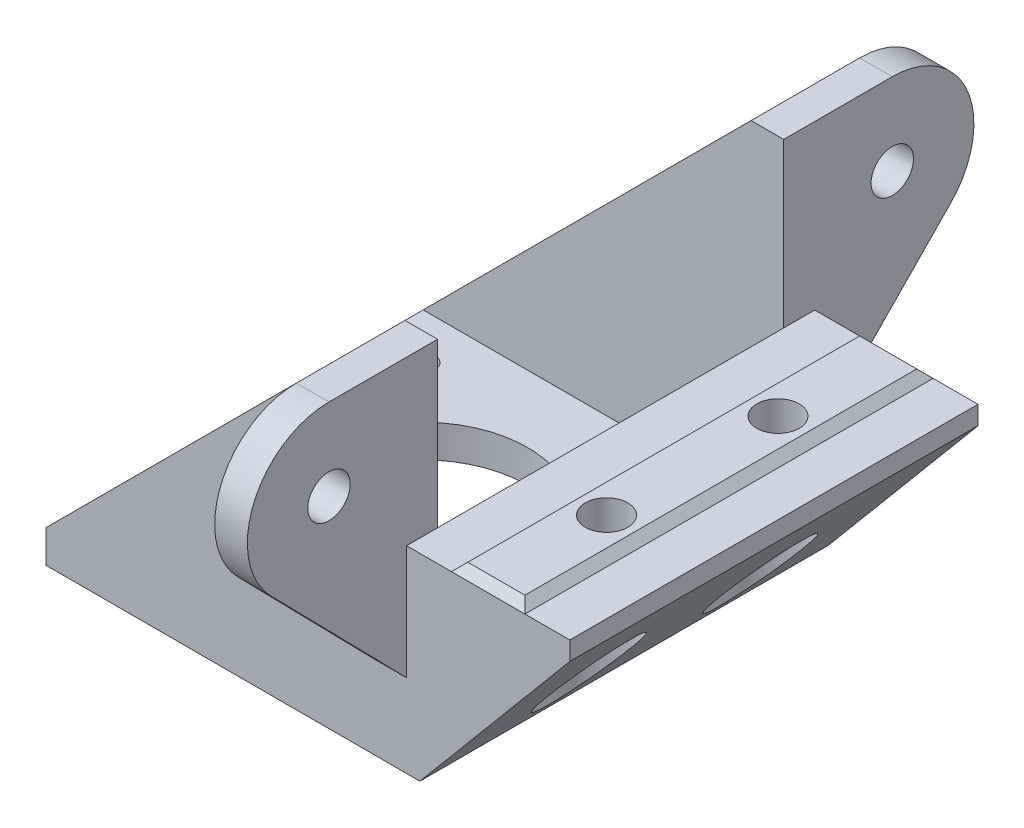
SolidWorks part; units mm, degrees
ref_plane "Front Plane" through (0, 0, 0) normal (0, 0, 1) x (1, 0, 0)
ref_plane "Top Plane" through (0, 0, 0) normal (0, 1, 0) x (1, 0, 0)
ref_plane "Right Plane" through (0, 0, 0) normal (1, 0, 0) x (0, 0, -1)
sketch "Sketch1" plane through (0, 0, 0) normal (0, 0, 1) x (1, 0, 0)
  line L0 (0, 0) -> (45.8, 0)
  line L1 (45.8, 0) -> (64.164, 21.8854)
  line L2 (64.164, 21.8854) -> (64.164, 24.164)
  line L3 (64.164, 24.164) -> (44.164, 24.164)
  line L4 (44.164, 44.164) -> (40.164, 44.164)
  line L5 (40.164, 44.164) -> (0, 4)
  line L6 (0, 4) -> (0, 0)
  line L7 (44.164, 24.164) -> (44.164, 44.164)
  dimension "D1" = 4
  dimension "D2" = 45.8
  dimension "D3" = 135
  dimension "D4" = 50
  dimension "D5" = 44.164
  dimension "D6" = 20
  dimension "D7" = 20
  dimension "D8" = 4
extrude "Boss-Extrude1" add sketch "Sketch1" against normal blind 3.8
sketch "Sketch2" plane through (0, 0, 0) normal (0, -1, 0) x (1, 0, 0)
  line L0 (0, 0) -> (45.8, 0)
  line L1 (45.8, 0) -> (45.8, -50)
  line L2 (45.8, -50) -> (0, -50)
  line L3 (0, -50) -> (0, 0)
  dimension "D1" = 50
extrude "Boss-Extrude2" add sketch "Sketch2" against normal blind 4
sketch "Sketch3" plane through (0, 0, -3.8) normal (0, 0, -1) x (-1, 0, 0)
  line L0 (-45.8, 4) -> (-49.1564, 4)
  line L1 (-49.1564, 4) -> (-45.8, 0)
  line L8 (-64.164, 21.8854) -> (-45.8, 0)
  line L9 (-45.8, 0) -> (-45.8, 4)
  line L10 (-45.8, 4) -> (0, 4)
  line L11 (0, 4) -> (-40.164, 44.164)
  line L12 (-40.164, 44.164) -> (-44.164, 44.164)
  line L13 (-44.164, 44.164) -> (-44.164, 24.164)
  line L14 (-44.164, 24.164) -> (-64.164, 24.164)
  line L15 (-64.164, 24.164) -> (-64.164, 21.8854)
  line L16 (-49.1564, 4) -> (-45.8, 0)
  line L17 (-45.8, 0) -> (-45.8, 4)
  line L19 (0, 4) -> (-40.164, 44.164)
  line L20 (-40.164, 44.164) -> (-44.164, 44.164)
  line L21 (-44.164, 44.164) -> (-44.164, 24.164)
  line L22 (-44.164, 24.164) -> (-64.164, 24.164)
  line L23 (-64.164, 24.164) -> (-64.164, 21.8854)
  line M9 (-64.164, 21.8854) -> (-45.8, 0)
  line M10 (-45.8, 0) -> (-45.8, 4)
  dimension "D1" = 0
extrude "Boss-Extrude3" add sketch "Sketch3" along normal through all contours L0 M10 M9
sketch "Sketch4" plane through (0, 0, -50) normal (0, 0, -1) x (-1, 0, 0)
  line L0 (-44.164, 24.164) -> (-44.164, 44.164) construction
  line L1 (-44.164, 44.164) -> (-40.164, 44.164) construction
  line L2 (-40.164, 44.164) -> (0, 4) construction
  line L3 (0, 4) -> (0, 0) construction
  line L4 (0, 0) -> (-45.8, 0) construction
  line L5 (-49.1564, 4) -> (-64.164, 21.8854) construction
  line L6 (-64.164, 21.8854) -> (-64.164, 24.164) construction
  line L7 (-64.164, 24.164) -> (-44.164, 24.164) construction
  line L8 (-44.164, 24.164) -> (-44.164, 44.164)
  line L9 (-44.164, 44.164) -> (-40.164, 44.164)
  line L10 (-40.164, 44.164) -> (0, 4)
  line L11 (0, 4) -> (0, 0)
  line L12 (0, 0) -> (-45.8, 0)
  line L13 (-45.8, 0) -> (-64.164, 21.8854)
  line L14 (-64.164, 21.8854) -> (-64.164, 24.164)
  line L15 (-64.164, 24.164) -> (-44.164, 24.164)
  point P8 (-46.9529, 1.374)
  point P13 (-45.9727, 0.2058)
extrude "Boss-Extrude4" add sketch "Sketch4" against normal blind 3.8
sketch "Sketch5" plane through (0, 0, 0) normal (0, 0, 1) x (1, 0, 0)
  line L0 (44.164, 24.164) -> (44.164, 0)
  line L1 (0, 0) -> (45.8, 0) construction
  line L2 (44.164, 0) -> (45.8, 0)
  line L3 (45.8, 0) -> (64.164, 21.8854)
  line L4 (64.164, 21.8854) -> (64.164, 24.164)
  line L5 (64.164, 24.164) -> (44.164, 24.164)
extrude "Boss-Extrude5" add sketch "Sketch5" against normal through all
sketch "Sketch6" plane through (0, 24.164, 0) normal (0, 1, 0) x (1, 0, 0)
  line L0 (44.164, 50) -> (64.164, 50) construction
  line L1 (49.664, 50) -> (58.664, 50)
  line L2 (49.664, 50) -> (49.664, 0)
  line L3 (49.664, 0) -> (58.664, 0)
  line L4 (58.664, 50) -> (58.664, 0)
  line L5 (64.164, 0) -> (44.164, 0) construction
  line L6 (64.164, 50) -> (64.164, 0) construction
  dimension "D1" = 9
  dimension "D2" = 5.5
extrude "Boss-Extrude6" add sketch "Sketch6" along normal blind 1 draft 45
sketch "Sketch7" plane through (44.164, 0, 0) normal (1, 0, 0) x (0, 0, -1)
  line L0 (50, 24.164) -> (0, 24.164) construction
  line L1 (0, 24.164) -> (0, 10.164)
  line L2 (46.2, 44.164) -> (46.2, 24.164)
  line L3 (0, 24.164) -> (50, 24.164) construction
  line L4 (46.2, 24.164) -> (50, 24.164)
  line L5 (50, 24.164) -> (50, 10.164)
  line L6 (50, 21.8854) -> (50, 0) construction
  line L7 (50, 10.164) -> (66.646, 27.1687)
  line L8 (46.2, 44.164) -> (59.5, 44.164)
  line L9 (3.8, 24.164) -> (0, 24.164)
  line L10 (25, 25.164) -> (25, 36.5675) construction
  line L11 (1, 25.164) -> (49, 25.164) construction
  line L12 (3.8, 44.164) -> (3.8, 24.164)
  line L13 (3.8, 44.164) -> (-9.5, 44.164)
  line L14 (0, 10.164) -> (-16.646, 27.1687)
  arc A0 (66.646, 27.1687) -> (59.5, 44.164) centre (59.5, 34.164) ccw
  circle A1 centre (59.5, 34.164) radius 2.6
  arc A2 (-16.646, 27.1687) -> (-9.5, 44.164) centre (-9.5, 34.164) cw
  circle A3 centre (-9.5, 34.164) radius 2.6
  dimension "D1" = 20
  dimension "D3" = 13.3
  dimension "D4" = 5.2
  dimension "D2" = 34
extrude "Boss-Extrude7" add sketch "Sketch7" against normal blind 4
sketch "Sketch8" plane through (0, 4, 0) normal (0, 1, 0) x (1, 0, 0)
  line L0 (0, 3.8) -> (0, 46.2) construction
  line L1 (44.164, 46.2) -> (0, 46.2) construction
  line L4 (44.164, 46.2) -> (44.164, 3.8) construction
  circle A0 centre (21, 25) radius 13
  circle A1 centre (5.5, 40.5) radius 1.6
  circle A2 centre (38.664, 40.5) radius 1.6
  circle A3 centre (38.664, 7.336) radius 1.6
  circle A4 centre (5.5, 7.336) radius 1.6
  point P16 (22.082, 23.918)
  dimension "D1" = 3.2
  dimension "D2" = 5.5
  dimension "D3" = 5.7
  dimension "D4" = 26
  dimension "D5" = 21
  dimension "D6" = 21.2
  dimension "D8" = 5.5
  dimension "D9" = 5.5
  dimension "D7" = 4
extrude "Cut-Extrude1" cut sketch "Sketch8" against normal up to next
sketch "Sketch9" plane through (0, 25.164, 0) normal (0, 1, 0) x (1, 0, 0)
  line L0 (50.664, 1) -> (57.664, 1) construction
  line L1 (57.664, 1) -> (57.664, 49) construction
  line L2 (57.664, 49) -> (50.664, 49) construction
  circle A0 centre (54.164, 14.5) radius 2.6
  circle A1 centre (54.164, 35.5) radius 2.6
  dimension "D1" = 5.2
  dimension "D2" = 5.2
  dimension "D3" = 13.5
  dimension "D4" = 3.5
  dimension "D5" = 3.5
  dimension "D6" = 13.5
extrude "Cut-Extrude2" cut sketch "Sketch9" against normal blind 4.8
sketch "Sketch10" plane through (0, 0, 0) normal (0, -1, 0) x (1, 0, 0)
  line L0 (64.164, -50) -> (45.8, -50) construction
  line L2 (45.8, -50) -> (45.8, 0) construction
  line L3 (45.8, 0) -> (64.164, 0) construction
  circle A0 centre (52, -14.5) radius 5
  circle A1 centre (52, -35.5) radius 5
  dimension "D1" = 14.5
  dimension "D2" = 10
  dimension "D3" = 10
  dimension "D4" = 6.2
  dimension "D5" = 6.2
  dimension "D6" = 14.5
extrude "Cut-Extrude3" cut sketch "Sketch10" against normal blind 20
